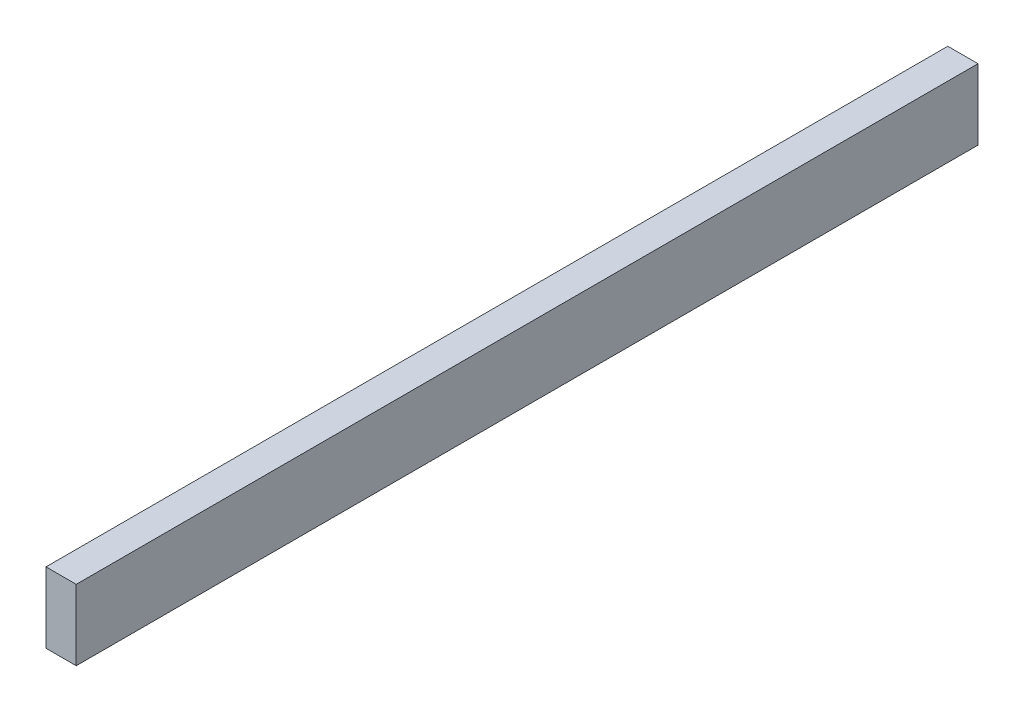
SolidWorks part; units mm, degrees
material "Pine"
ref_plane "Front Plane" through (0, 0, 0) normal (0, 0, 1) x (1, 0, 0)
ref_plane "Top Plane" through (0, 0, 0) normal (0, 1, 0) x (1, 0, 0)
ref_plane "Right Plane" through (0, 0, 0) normal (1, 0, 0) x (0, 0, -1)
sketch "Sketch1" plane through (0, 0, 0) normal (0, 0, 1) x (1, 0, 0)
  line L1 (-38.1, 57.3854) -> (0, 57.3854)
  line L2 (-38.1, 57.3854) -> (-38.1, -31.5146)
  line L3 (-38.1, -31.5146) -> (0, -31.5146)
  line L4 (0, 57.3854) -> (0, -31.5146)
  dimension "D1" = 38.1
  dimension "D2" = 88.9
extrude "Boss-Extrude1" add sketch "Sketch1" along normal blind 1136.65
